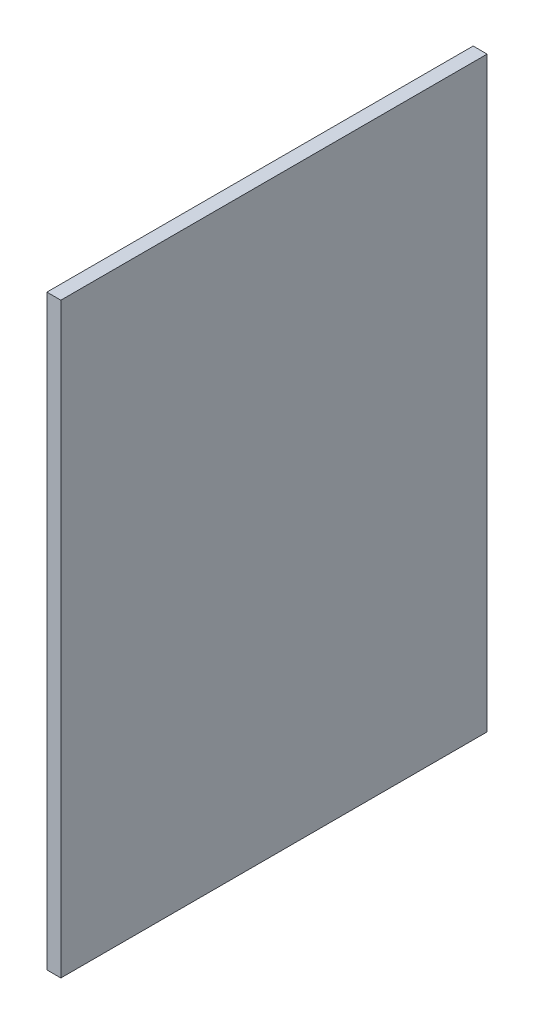
SolidWorks part; units mm, degrees
ref_plane "Front Plane" through (0, 0, 0) normal (0, 0, 1) x (1, 0, 0)
ref_plane "Top Plane" through (0, 0, 0) normal (0, 1, 0) x (1, 0, 0)
ref_plane "Right Plane" through (0, 0, 0) normal (1, 0, 0) x (0, 0, -1)
sketch "Sketch1" plane through (0, 0, 0) normal (0, 1, 0) x (1, 0, 0)
  line L0 (169.8625, 0) -> (169.8625, 173.0375) construction
  line L1 (173.0375, 173.0375) -> (0, 173.0375)
  line L2 (173.0375, 173.0375) -> (173.0375, 0)
  line L3 (-173.0375, 0) -> (-50.8, 0)
  line L4 (0, 50.8) -> (0, 173.0375)
  arc A0 (-169.8625, 0) -> (169.8625, 0) centre (0, 0) ccw construction
  arc A1 (173.0375, 0) -> (-173.0375, 0) centre (0, 0) cw
  arc A2 (-50.8, 0) -> (0, 50.8) centre (0, 0) cw
  dimension "D1" = 169.8625
  dimension "D2" = 3.175
  dimension "D4" = 50.8
  dimension "D3" = 3.175
sketch "Sketch7" plane through (0, 0, 0) normal (0, 1, 0) x (1, 0, 0)
  line L1 (169.8625, 0) -> (169.8625, 173.0375)
  line L3 (169.8625, 173.0375) -> (173.0375, 173.0375)
  line L5 (173.0375, 0) -> (173.0375, 173.0375)
  line L6 (-169.8625, 0) -> (-173.0375, 0)
  line L8 (39.6875, 173.0375) -> (42.8625, 173.0375)
  line L9 (39.6875, 173.0375) -> (39.6875, 76.2)
  line L10 (39.6875, 76.2) -> (42.8625, 76.2)
  line L11 (42.8625, 173.0375) -> (42.8625, 76.2)
  line L12 (173.0375, 173.0375) -> (173.0375, 0) construction
  line L13 (173.0375, 173.0375) -> (0, 173.0375) construction
  arc A0 (-169.8625, 0) -> (169.8625, 0) centre (0, 0) ccw
  arc A2 (-173.0375, 0) -> (173.0375, 0) centre (0, 0) ccw
  arc A3 (-173.0375, 0) -> (173.0375, 0) centre (0, 0) ccw construction
  point P9 (188.655, 176.6864)
  dimension "D1" = 3.175
  dimension "D2" = 3.175
  dimension "D3" = 127
  dimension "D4" = 76.2
extrude "Boss-Extrude1" add sketch "Sketch7" along normal mid plane 133.35 contours L9 L10 L11 L8
